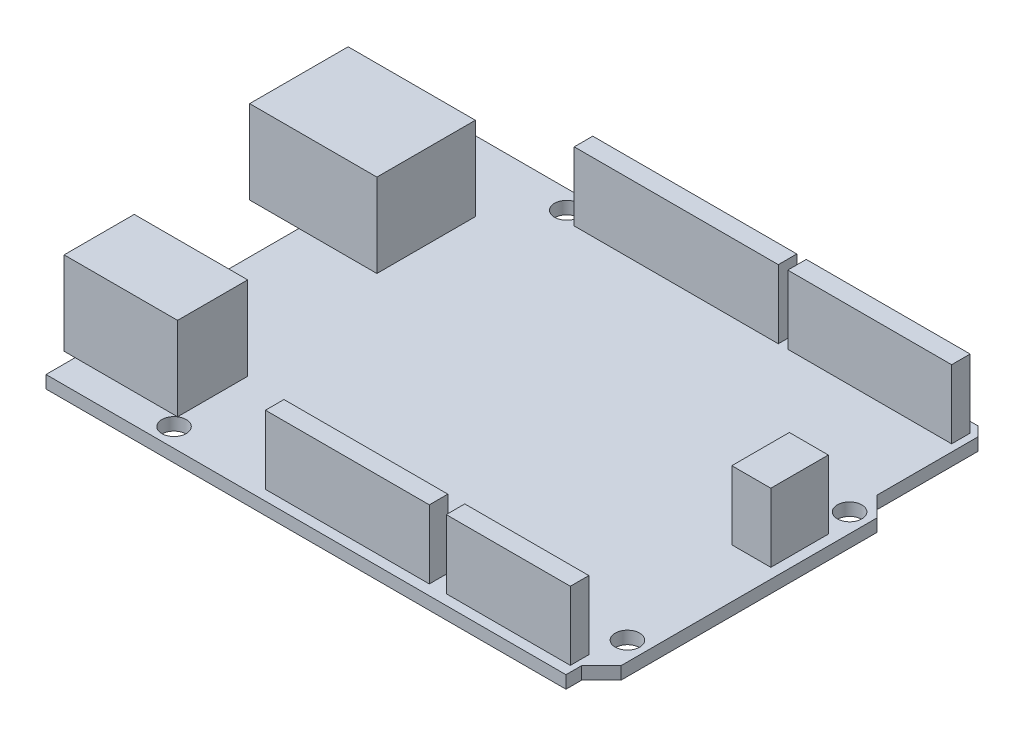
SolidWorks part; units mm, degrees
ref_plane "Front" through (0, 0, 0) normal (0, 0, 1) x (1, 0, 0)
ref_plane "Top" through (0, 0, 0) normal (0, 1, 0) x (1, 0, 0)
ref_plane "Right" through (0, 0, 0) normal (1, 0, 0) x (0, 0, -1)
sketch "Sketch1" plane through (0, 0, 0) normal (0, 1, 0) x (1, 0, 0)
  line L0 (66, 52.2979) -> (66, 39.5)
  line L1 (0, 0) -> (66, 0)
  line L2 (0, 0) -> (0, 53.5)
  line L3 (0, 53.5) -> (64.7979, 53.5)
  line L4 (68.5, 4.5) -> (68.5, 37)
  line L7 (66, 39.5) -> (68.5, 37)
  line L8 (66, 2) -> (66, 0)
  line L9 (66, 2) -> (68.5, 4.5)
  line L10 (64.7979, 53.5) -> (66, 52.2979)
  circle A0 centre (15, 51.1) radius 1.55
  circle A1 centre (66.1, 35.9) radius 1.55
  circle A2 centre (66.1, 7.7) radius 1.55
  circle A3 centre (13.85, 2.4) radius 1.55
  point P0 (0, 0)
  dimension "D4" = 3.1
  dimension "D1" = 68.5
  dimension "D2" = 53.5
  dimension "D3" = 66
  dimension "D5" = 135
  dimension "D6" = 2
  dimension "D7" = 135
  dimension "D8" = 15
  dimension "D9" = 13.85
  dimension "D10" = 2.4
  dimension "D11" = 2.4
  dimension "D12" = 2.4
  dimension "D13" = 17.6
  dimension "D14" = 7.7
  dimension "D15" = 135
  dimension "D16" = 1.7
  dimension "D17" = 32.5
extrude "Boss-Extrude1" add sketch "Sketch1" along normal blind 1.6
sketch "Sketch2" plane through (0, 1.6, 0) normal (0, 1, 0) x (1, 0, 0)
  line L0 (66, 39.5) -> (66, 52.2979) construction
  line L1 (17.2, 52.2) -> (43.1, 52.2)
  line L2 (17.2, 52.2) -> (17.2, 49.85)
  line L3 (17.2, 49.85) -> (43.1, 49.85)
  line L4 (43.1, 52.2) -> (43.1, 49.85)
  line L5 (44.3, 52.2) -> (65.1, 52.2)
  line L6 (44.3, 52.2) -> (44.3, 49.85)
  line L7 (44.3, 49.85) -> (65.1, 49.85)
  line L8 (65.1, 52.2) -> (65.1, 49.85)
  line L9 (64.7979, 53.5) -> (0, 53.5) construction
  line L10 (66, 0) -> (66, 2) construction
  line L11 (65.2537, 1.3) -> (49.5037, 1.3)
  line L12 (65.2537, 1.3) -> (65.2537, 3.65)
  line L13 (65.2537, 3.65) -> (49.5037, 3.65)
  line L14 (49.5037, 1.3) -> (49.5037, 3.65)
  line L15 (47.3537, 3.65) -> (26.5537, 3.65)
  line L16 (47.3537, 3.65) -> (47.3537, 1.3)
  line L17 (47.3537, 1.3) -> (26.5537, 1.3)
  line L18 (26.5537, 3.65) -> (26.5537, 1.3)
  line L19 (0, 0) -> (66, 0) construction
  line L20 (68.5, 4.5) -> (68.5, 37) construction
  line L21 (62.25, 32.1) -> (67.2, 32.1)
  line L22 (62.25, 32.1) -> (62.25, 24.8)
  line L23 (62.25, 24.8) -> (67.2, 24.8)
  line L24 (67.2, 32.1) -> (67.2, 24.8)
  dimension "D1" = 2.35
  dimension "D2" = 20.8
  dimension "D3" = 25.9
  dimension "D4" = 1.2
  dimension "D5" = 0.9
  dimension "D6" = 1.3
  dimension "D7" = 15.75
  dimension "D8" = 2.15
  dimension "D9" = 20.8
  dimension "D10" = 0.7463
  dimension "D11" = 1.3
  dimension "D12" = 4.95
  dimension "D13" = 7.3
  dimension "D14" = 1.3
  dimension "D15" = 24.8
extrude "Boss-Extrude2" add sketch "Sketch2" along normal blind 8.7
sketch "Sketch3" plane through (0, 1.6, 0) normal (0, 1, 0) x (1, 0, 0)
  line L0 (64.7979, 53.5) -> (0, 53.5) construction
  line L1 (9.9, 32.1) -> (-6.25, 32.1)
  line L2 (9.9, 32.1) -> (9.9, 44.6)
  line L3 (9.9, 44.6) -> (-6.25, 44.6)
  line L4 (-6.25, 32.1) -> (-6.25, 44.6)
  line L5 (0, 53.5) -> (0, 0) construction
  line L6 (0, 0) -> (66, 0) construction
  line L7 (-1.4, 12.6) -> (13, 12.6)
  line L8 (-1.4, 12.6) -> (-1.4, 3.7)
  line L9 (-1.4, 3.7) -> (13, 3.7)
  line L10 (13, 12.6) -> (13, 3.7)
  dimension "D1" = 16.15
  dimension "D2" = 12.5
  dimension "D3" = 8.9
  dimension "D4" = 6.25
  dimension "D5" = 14.4
  dimension "D6" = 8.9
  dimension "D7" = 1.4
  dimension "D8" = 3.7
extrude "Boss-Extrude3" add sketch "Sketch3" along normal blind 10.6
